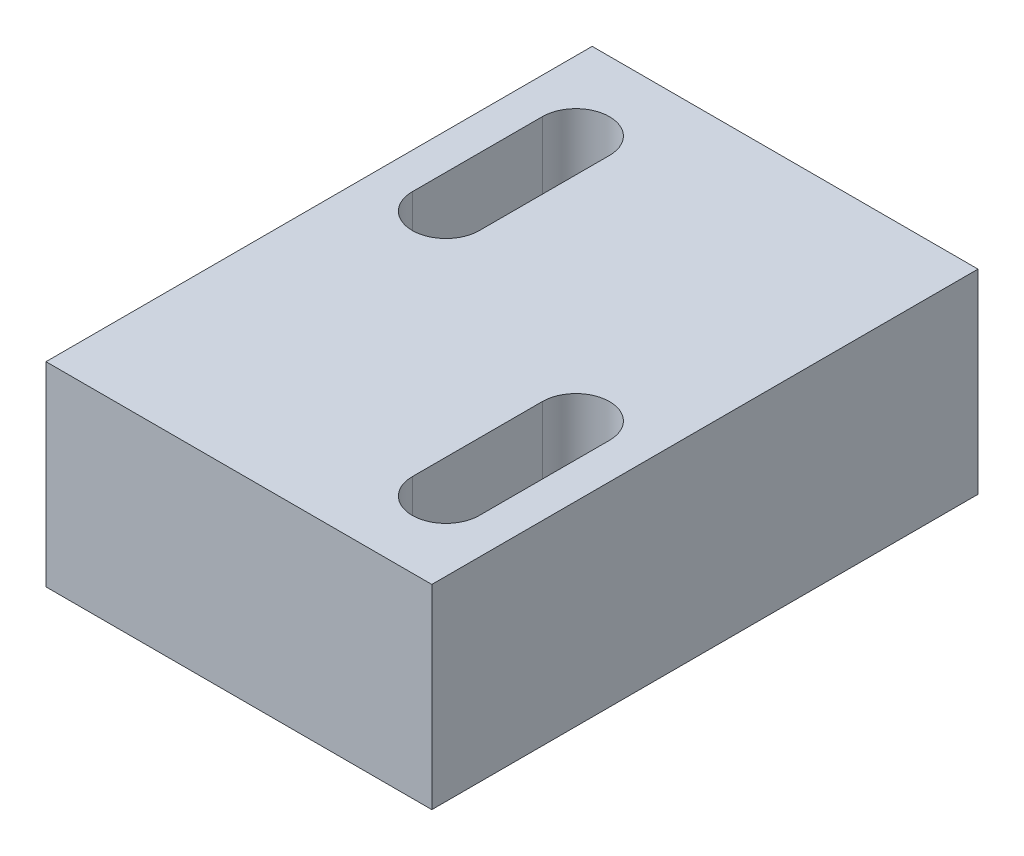
SolidWorks part; units mm, degrees
ref_plane "Alzado" through (0, 0, 0) normal (0, 0, 1) x (1, 0, 0)
ref_plane "Planta" through (0, 0, 0) normal (0, 1, 0) x (1, 0, 0)
ref_plane "Vista lateral" through (0, 0, 0) normal (1, 0, 0) x (0, 0, -1)
sketch "Croquis1" plane through (0, 0, 0) normal (0, 1, 0) x (1, 0, 0)
  line L1 (-17.5, -12.6) -> (17.5, -12.6)
  line L2 (-17.5, -12.6) -> (-17.5, 12.6)
  line L3 (-17.5, 12.6) -> (17.5, 12.6)
  line L4 (17.5, -12.6) -> (17.5, 12.6)
  line L5 (-17.5, -12.6) -> (17.5, 12.6) construction
  line L6 (-17.5, 12.6) -> (17.5, -12.6) construction
  point P0 (0, 0)
  dimension "D1" = 35
  dimension "D2" = 25.2
extrude "Saliente-Extruir1" add sketch "Croquis1" along normal blind 9
sketch "Croquis2" plane through (0, 0, 0) normal (0, -1, 0) x (1, 0, 0)
  line L0 (-4.4572, 2.7437) -> (-4.4572, 8.7437) construction
  line L1 (-1.3572, 2.7437) -> (-1.3572, 8.7437) construction
  line L2 (-12.7409, -8.64) -> (-12.7409, -2.64) construction
  line L3 (-15.8409, -8.64) -> (-15.8409, -2.64) construction
  line L4 (-4.4572, 2.7437) -> (-4.4572, 8.7437)
  line L5 (-1.3572, 2.7437) -> (-1.3572, 8.7437)
  line L6 (-12.7409, -8.64) -> (-12.7409, -2.64)
  line L7 (-15.8409, -8.64) -> (-15.8409, -2.64)
  arc A0 (-1.3572, 8.7437) -> (-4.4572, 8.7437) centre (-2.9072, 8.7437) ccw construction
  arc A1 (-12.7409, -2.64) -> (-15.8409, -2.64) centre (-14.2909, -2.64) ccw construction
  arc A2 (-1.3572, 8.7437) -> (-4.4572, 8.7437) centre (-2.9072, 8.7437) ccw
  arc A3 (-12.7409, -2.64) -> (-15.8409, -2.64) centre (-14.2909, -2.64) ccw
  arc A4 (-4.4572, 2.7437) -> (-1.3572, 2.7437) centre (-2.9072, 2.7437) ccw construction
  arc A6 (-4.4572, 2.7437) -> (-1.3572, 2.7437) centre (-2.9072, 2.7437) ccw
  arc A8 (-15.8409, -8.64) -> (-12.7409, -8.64) centre (-14.2909, -8.64) ccw construction
  arc A9 (-15.8409, -8.64) -> (-12.7409, -8.64) centre (-14.2909, -8.64) ccw
extrude "Cortar-Extruir1" cut sketch "Croquis2" against normal through all
sketch "Croquis3" plane through (0, 0, 0) normal (0, -1, 0) x (1, 0, 0)
  line L0 (-17.5, 12.6) -> (17.5, 12.6) construction
  line L1 (17.5, -12.6) -> (0.3019, -12.6)
  line L2 (17.5, -12.6) -> (17.5, 12.6)
  line L3 (17.5, 12.6) -> (0.3019, 12.6)
  line L4 (0.3019, -12.6) -> (0.3019, 12.6)
  line L5 (-17.5, -5.64) -> (-15.8409, -5.64) construction
  line L6 (-17.5, -12.6) -> (-17.5, 12.6) construction
  line L7 (-15.8409, -2.64) -> (-15.8409, -8.64) construction
  line L9 (-1.3572, 2.7437) -> (-1.3572, 8.7437) construction
  line L10 (-1.3572, 5.7437) -> (0.3019, 5.7437) construction
extrude "Cortar-Extruir2" cut sketch "Croquis3" against normal through all
